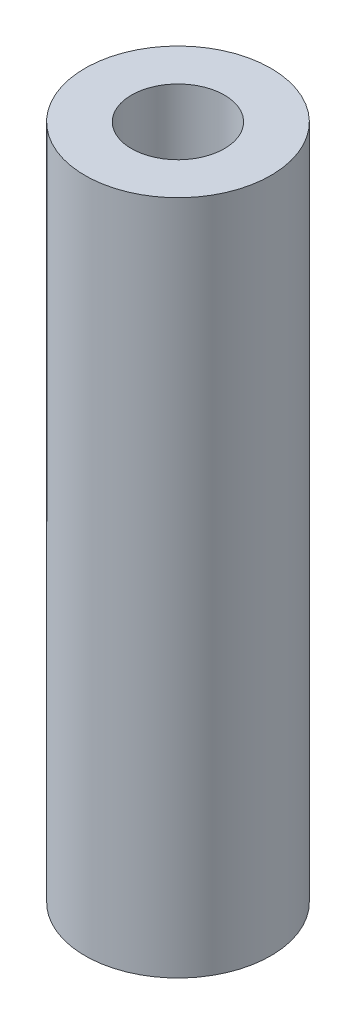
SolidWorks part; units mm, degrees
ref_plane "Front Plane" through (0, 0, 0) normal (0, 0, 1) x (1, 0, 0)
ref_plane "Top Plane" through (0, 0, 0) normal (0, 1, 0) x (1, 0, 0)
ref_plane "Right Plane" through (0, 0, 0) normal (1, 0, 0) x (0, 0, -1)
sketch "Sketch1" plane through (0, 0, 0) normal (0, 0, 1) x (1, 0, 0)
  line L0 (0, 0) -> (0, 80) construction
  line L2 (5.5, 0) -> (11, 0)
  line L3 (5.5, 0) -> (5.5, 80)
  line L4 (5.5, 80) -> (11, 80)
  line L5 (11, 0) -> (11, 80)
  dimension "D1" = 80
  dimension "D2" = 5.5
  dimension "D3" = 11
revolve "Revolve1" add sketch "Sketch1" angle 360 about L0
